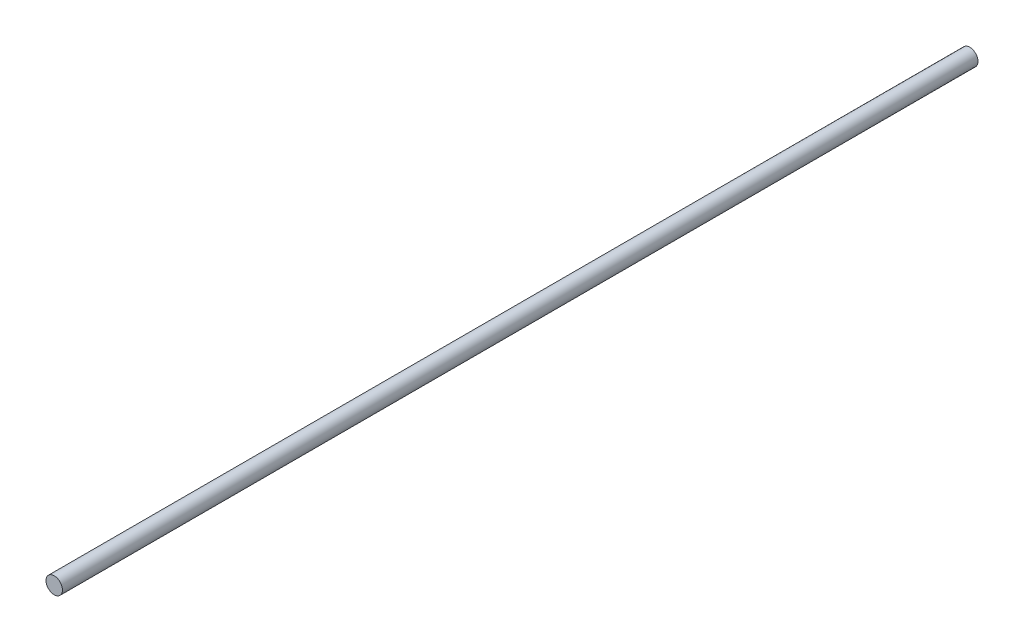
SolidWorks part; units mm, degrees
ref_plane "Alzado" through (0, 0, 0) normal (0, 0, 1) x (1, 0, 0)
ref_plane "Planta" through (0, 0, 0) normal (0, 1, 0) x (1, 0, 0)
ref_plane "Vista lateral" through (0, 0, 0) normal (1, 0, 0) x (0, 0, -1)
sketch "Croquis1" plane through (0, 0, 0) normal (0, 0, 1) x (1, 0, 0)
  circle A0 centre (0, 0) radius 0.9
  dimension "D1" = 1.8
extrude "Saliente-Extruir1" add sketch "Croquis1" along normal mid plane 100
